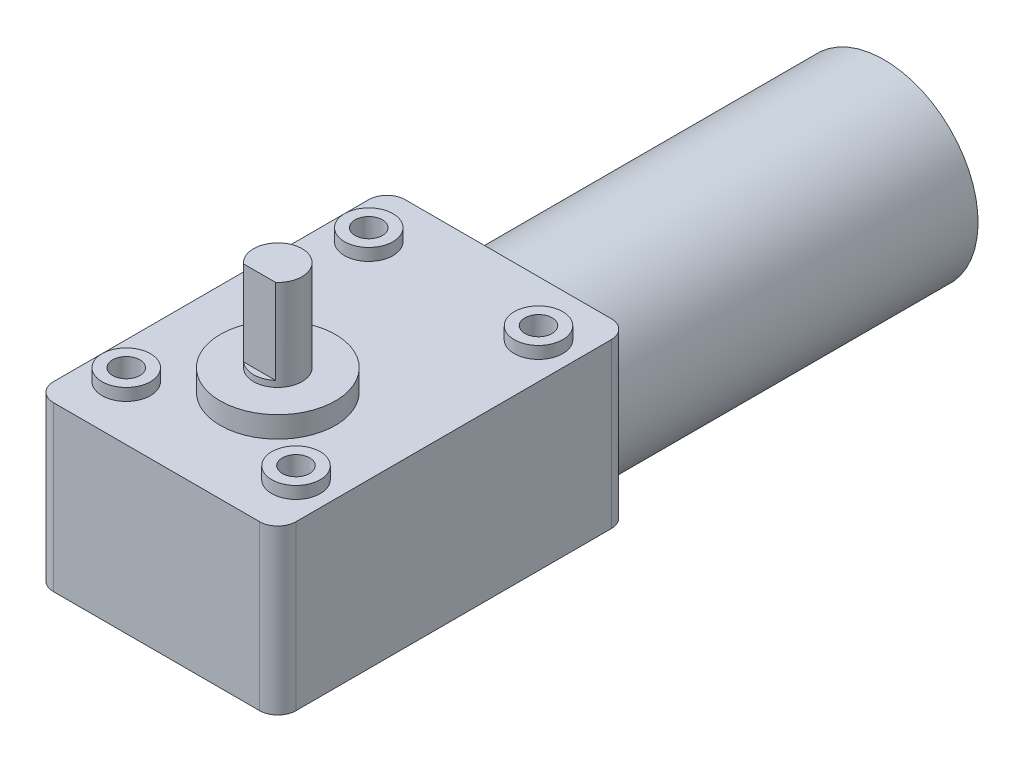
SolidWorks part; units mm, degrees
ref_plane "Front Plane" through (0, 0, 0) normal (0, 0, 1) x (1, 0, 0)
ref_plane "Top Plane" through (0, 0, 0) normal (0, 1, 0) x (1, 0, 0)
ref_plane "Right Plane" through (0, 0, 0) normal (1, 0, 0) x (0, 0, -1)
sketch "Sketch1" plane through (0, 0, 0) normal (0, 1, 0) x (0, 0, -1)
  line L0 (44.1242, 20) -> (80.0954, 20) construction
  line L1 (3, 0) -> (55, 0)
  line L2 (0, 3) -> (0, 37)
  line L3 (3, 40) -> (55, 40)
  line L4 (58, 3) -> (58, 37)
  arc A0 (3, 0) -> (0, 3) centre (3, 3) cw
  arc A1 (55, 0) -> (58, 3) centre (55, 3) ccw
  arc A2 (55, 40) -> (58, 37) centre (55, 37) cw
  arc A3 (0, 37) -> (3, 40) centre (3, 37) cw
  circle A4 centre (9, 34) radius 2
  circle A5 centre (20, 20) radius 9.5
  circle A10 centre (49, 34) radius 2
  circle A11 centre (49, 6) radius 2
  circle A12 centre (9, 6) radius 2
  circle A13 centre (20, 20) radius 4
  point P7 (0, 0)
  point P12 (58, 40)
  point P15 (0, 40)
  point P24 (58, 20)
  point P25 (0, 0)
  dimension "D3" = 3
  dimension "D8" = 19
  dimension "D9" = 4
  dimension "D10" = 8
  dimension "D1" = 40
  dimension "D2" = 58
  dimension "D4" = 9
  dimension "D5" = 11
  dimension "D6" = 2
  dimension "D7" = 2
extrude "Boss-Extrude2" add sketch "Sketch1" along normal blind 27
sketch "Sketch2" plane through (0, 27, 0) normal (0, 1, 0) x (1, 0, 0)
  line L4 (-3, 58) -> (-37, 58)
  line L5 (-40, 55) -> (-40, 3)
  line L6 (-37, 0) -> (-3, 0)
  line L7 (0, 3) -> (0, 55)
  line L8 (-3, 58) -> (-37, 58)
  line L9 (-40, 55) -> (-40, 3)
  line L10 (-37, 0) -> (-3, 0)
  line L11 (0, 3) -> (0, 55)
  arc A4 (-37, 58) -> (-40, 55) centre (-37, 55) ccw
  arc A5 (-40, 3) -> (-37, 0) centre (-37, 3) ccw
  arc A6 (-3, 0) -> (0, 3) centre (-3, 3) ccw
  arc A7 (0, 55) -> (-3, 58) centre (-3, 55) ccw
  arc A8 (-37, 58) -> (-40, 55) centre (-37, 55) ccw
  arc A9 (-40, 3) -> (-37, 0) centre (-37, 3) ccw
  arc A10 (-3, 0) -> (0, 3) centre (-3, 3) ccw
  arc A11 (0, 55) -> (-3, 58) centre (-3, 55) ccw
  circle A16 centre (-20, 20) radius 9.5 construction
  circle A17 centre (-20, 20) radius 9.5
  circle A18 centre (-34, 49) radius 4
  circle A19 centre (-6, 49) radius 4
  circle A20 centre (-6, 9) radius 4
  circle A21 centre (-34, 9) radius 4
  dimension "D2" = 8
  dimension "D3" = 8
  dimension "D4" = 8
  dimension "D5" = 8
  dimension "D1" = 0
extrude "Boss-Extrude3" add sketch "Sketch2" along normal blind 2 contours A21 | A20 | A19 | A18
sketch "Sketch3" plane through (0, 27, 0) normal (0, 1, 0) x (1, 0, 0)
  line L0 (-20, 63.9597) -> (-20, 52.4494) construction
  circle A0 centre (-20, 20) radius 9.5
  point P3 (0, 0)
extrude "Boss-Extrude4" add sketch "Sketch3" along normal blind 3.5
sketch "Sketch4" plane through (0, 30.5, 0) normal (0, 1, 0) x (1, 0, 0)
  circle A0 centre (-20, 20) radius 4
extrude "Boss-Extrude5" add sketch "Sketch4" along normal blind 1
sketch "Sketch5" plane through (0, 31.5, 0) normal (0, 1, 0) x (1, 0, 0)
  line L0 (-22.6458, 17) -> (-17.3542, 17)
  arc A0 (-17.3542, 17) -> (-22.6458, 17) centre (-20, 20) ccw
  dimension "D1" = 8
  dimension "D2" = 3
extrude "Boss-Extrude6" add sketch "Sketch5" along normal blind 14
hole_wizard "M4 Clearance Hole1" positions "Sketch6" profile "Sketch7" hole size "M4" standard "ANSI Metric"
sketch "Sketch6" plane through (0, 29, 0) normal (0, 1, 0) x (1, 0, 0)
  point P0 (-34, 9)
  point P3 (-34, 49)
  point P6 (-6, 49)
  point P9 (-6, 9)
sketch "Sketch7" plane through (-34, 29, -9) normal (1, 0, 0) x (0, 0, 1)
  line L0 (0, 0) -> (0, 10.3519)
  line L1 (0, 10.3519) -> (2.25, 9)
  line L2 (2.25, 9) -> (2.25, 0)
  line L5 (2.25, 0) -> (0, 0)
  line L10 (0, 10.3519) -> (-2.25, 9) construction
  line L11 (0, -6.35) -> (0, 107.95) construction
  dimension "Hole Dia." = 4.5
  dimension "Hole Depth" = 9
  dimension "Drill Angle" = 118
sketch "Sketch8" plane through (0, 0, -58) normal (0, 0, -1) x (-1, 0, 0)
  line L0 (3, 27) -> (37, 27) construction
  circle A0 centre (20, 9) radius 15.5
  dimension "D2" = 31
  dimension "D1" = 18
extrude "Boss-Extrude7" add sketch "Sketch8" along normal blind 62
sketch "Sketch9" plane through (0, 0, -120) normal (0, 0, -1) x (-1, 0, 0)
  circle A0 centre (20, 9) radius 7.5
  dimension "D1" = 15
extrude "Boss-Extrude8" add sketch "Sketch9" along normal blind 2
